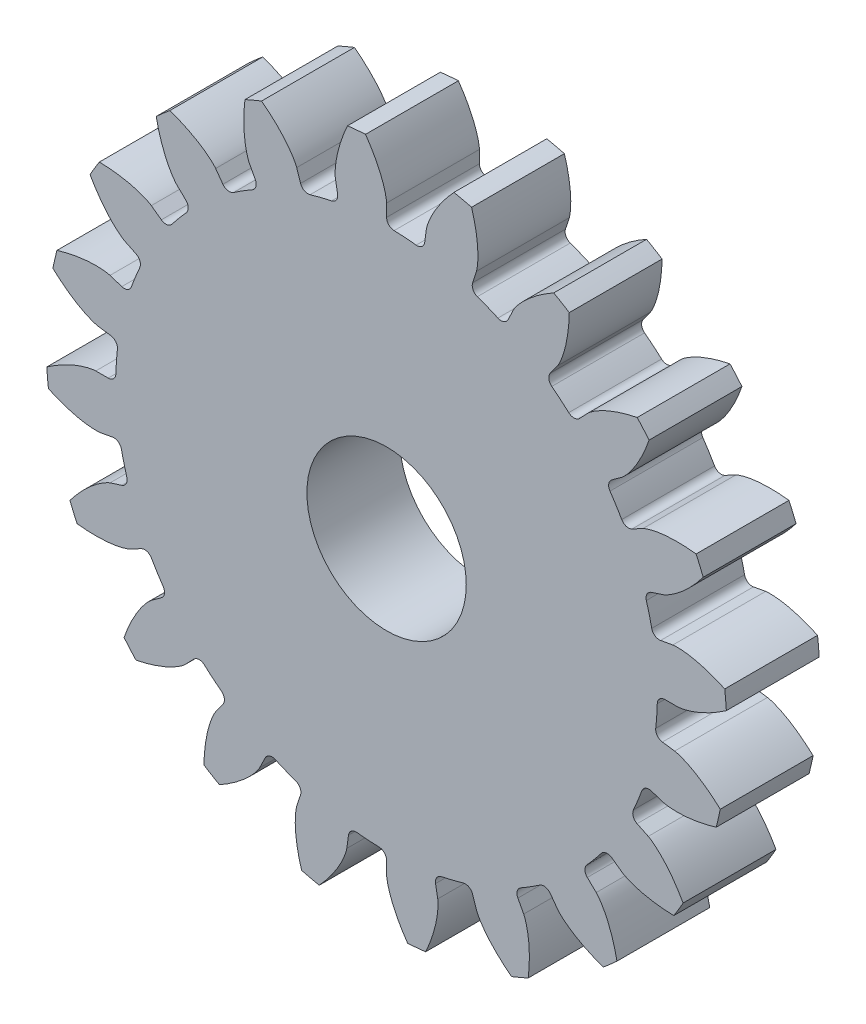
SolidWorks part; units mm, degrees
ref_plane "Front Plane" through (0, 0, 0) normal (0, 0, 1) x (1, 0, 0)
ref_plane "Top Plane" through (0, 0, 0) normal (0, 1, 0) x (1, 0, 0)
ref_plane "Right Plane" through (0, 0, 0) normal (1, 0, 0) x (0, 0, -1)
sketch "Sketch1" plane through (0, 0, 0) normal (0, 0, 1) x (1, 0, 0)
  line L0 (9.3969, 0) -> (8.75, 0)
  line L1 (10.957, 0.9716) -> (-10.957, -0.9716)
  line L2 (0, 0) -> (9.9989, 0.149) construction
  circle A0 centre (0, 0) radius 9.3969 construction
  circle A1 centre (0, 0) radius 11
  circle A2 centre (0, 0) radius 8.75
  circle A3 centre (0, 0) radius 10 construction
  spline S0 degree 4 poles (9.3969, 0) (9.4039, 0.0001) (9.4233, 0.001) (9.4601, 0.0044) (9.5198, 0.0126) (9.5953, 0.0267) (9.6923, 0.0492) (9.8055, 0.0811) (9.9285, 0.1217) (10.0606, 0.172) (10.1907, 0.2274) (10.3189, 0.2874) (10.4449, 0.3516) (10.5954, 0.4343) (10.7729, 0.5404) (10.9755, 0.6744) (11.1993, 0.8377) (11.4205, 1.016) (11.6321, 1.2011) (11.8386, 1.3988) (12.0332, 1.5975) (12.2272, 1.8143) (12.4021, 2.0197) (12.5886, 2.2606) (12.7364, 2.4583) (12.9206, 2.73) (13.0263, 2.8938) (13.1461, 3.089) (13.1973, 3.1776) (13.2289, 3.2321) knots 0 0 0 0 0 0.005377 0.015084 0.028532 0.04661 0.064855 0.092111 0.119476 0.146842 0.174209 0.201575 0.228941 0.256307 0.307035 0.361767 0.4165 0.471232 0.525964 0.580697 0.635429 0.690161 0.744894 0.799626 0.854358 0.909091 0.954545 1 1 1 1 1 construction
  spline S1 degree 4 poles (9.3969, 0) (9.4039, 0.0001) (9.4233, 0.001) (9.4601, 0.0044) (9.5198, 0.0126) (9.5953, 0.0267) (9.6923, 0.0492) (9.8055, 0.0811) (9.9285, 0.1217) (10.0606, 0.172) (10.1907, 0.2274) (10.3189, 0.2874) (10.4449, 0.3516) (10.5954, 0.4343) (10.7729, 0.5404) (10.9755, 0.6744) (11.1993, 0.8377) (11.4205, 1.016) (11.6321, 1.2011) (11.8386, 1.3988) (12.0332, 1.5975) (12.2272, 1.8143) (12.4021, 2.0197) (12.5886, 2.2606) (12.7364, 2.4583) (12.8807, 2.6711) (12.9497, 2.776) (12.9844, 2.8301) knots 0 0 0 0 0 0.005377 0.015084 0.028532 0.04661 0.064855 0.092111 0.119476 0.146842 0.174209 0.201575 0.228941 0.256307 0.307035 0.361767 0.4165 0.471232 0.525964 0.580697 0.635429 0.690161 0.744894 0.799626 0.854358 0.909091 0.909091 0.909091 0.909091 0.909091
  dimension "D1" = 18.7939
  dimension "D2" = 22
  dimension "D3" = 17.5
  dimension "D5" = 20
  dimension "D4" = 4.214
extrude "Boss-Extrude3" add sketch "Sketch1" along normal blind 3 contours L1 A2 | A2 L1 | L0 S1 A1 L1 A2
mirror "Mirror2" about plane through (0, 0, 3) normal (0.0883, -0.9961, 0) of "Boss-Extrude3"
fillet "Fillet1" radius 0.25 2 edges at (8.6135, 1.5397, 1.5) (8.75, 0, 1.5)
pattern_circular "CirPattern8" count 20 over 360 about axis through (0, 0, 3) along (0, 0, -1) of "Boss-Extrude3", "Mirror2", "Fillet1"
sketch "Sketch3" plane through (0, 0, 3) normal (0, 0, 1) x (1, 0, 0)
  circle A0 centre (0, 0) radius 2.575
  dimension "D1" = 5.15
extrude "Cut-Extrude2" cut sketch "Sketch3" against normal through all
sketch "Sketch4" plane through (0, 0, 3) normal (0, 0, 1) x (1, 0, 0)
  circle A0 centre (0, 0) radius 5
  circle A1 centre (0, 0) radius 2.575
  dimension "D1" = 10
  dimension "D2" = 5.15
extrude "Boss-Extrude4" [suppressed] add sketch "Sketch4" along normal blind 1
equation "\"d\"= 20'Pitch diameter"
equation "\"N\"= 20'Number of teeth"
equation "\"bl\"= 0.1mm'Backlash"
equation "\"pa\"= 20deg'Pressure angle (deg)"
equation "\"pc\"= ( 3.1415 * \"d\" ) / \"N\"\t'Circular pitch"
equation "\"m\"= \"d\" / \"N\"\t\t\t'module"
equation "\"P\"= \"N\" / \"d\"\t\t\t'Diametral pitch"
equation "\"a\"= 1/\"P\"\t\t\t'Addendum distance"
equation "\"b\"= 1.25 / \"P\"'Dedendum distance"
equation "\"rb\"= (\"d\"/2)*cos(\"pa\")\t\t'base circle radius"
equation "\"cp\"= 3.1415/\"P\"\t\t'Circular pitch"
equation "\"t\"= ( \"cp\" / 2 ) - \"bl\"'tooth tickness"
equation "\"c\"=\"b\"-\"a\"\t\t\t'Clearance"
equation "\"facewidth\"= 3'face width"
equation "\"rbd\"= \"rb\" * 2'base circle diameter"
equation "\"D1@Sketch1\"=\"rbd\""
equation "\"D2@Sketch1\"= \"d\" + (\"a\" * 2)"
equation "\"D3@Sketch1\" = \"ded\""
equation "\"D4@Sketch1\"= ((\"t\" /2) / (\"d\"/2)) * (180/3.1415)"
equation "\"D1@Boss-Extrude3\"=\"facewidth\""
equation "\"D1@Fillet1\"=\"c\""
equation "\"D1@CirPattern8\"=\"N\""
equation "\"D5@Sketch1\"=\"d\""
equation "\"ded1\"= \"d\" - 2 * ( ( ( \"d\" / 2 ) - \"rb\" ) + ( 0.5 * ( 1.25 / \"P\" ) ) )"
equation "\"ded2\"= \"d\" - ( \"b\" * 2 )"
equation "\"ded\"= IIF ( \"rb\" < ( \"ded2\" / 2 ) , \"ded1\" , \"ded2\" )"
equation "\"shaftdia\"= 5.15"
equation "\"D1@Sketch3\"=\"shaftdia\""
